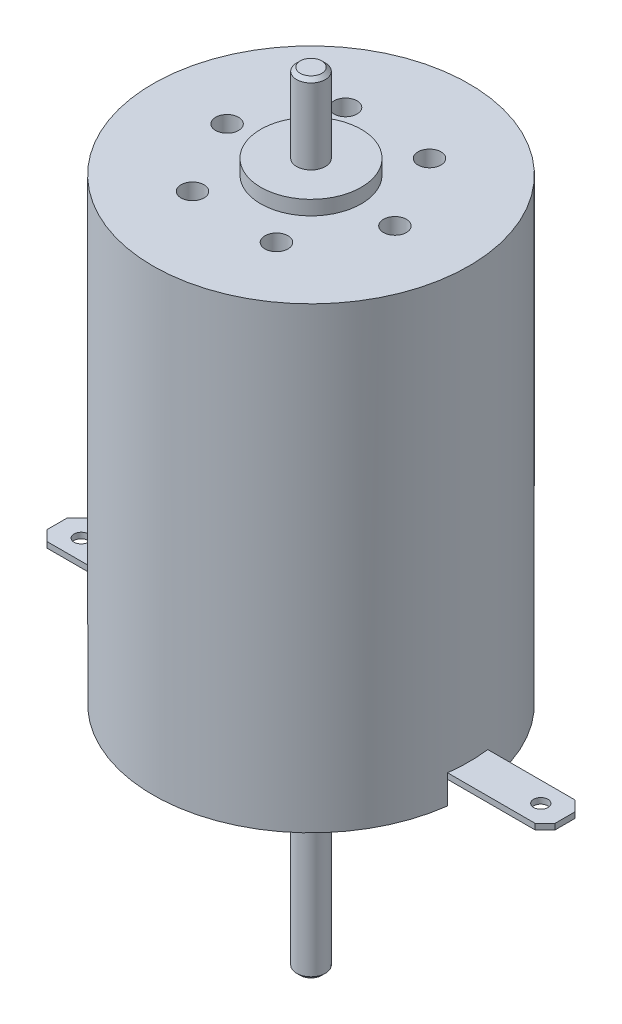
SolidWorks part; units mm, degrees
ref_plane "Face" through (0, 0, 0) normal (0, 0, 1) x (1, 0, 0)
ref_plane "Dessus" through (0, 0, 0) normal (0, 1, 0) x (1, 0, 0)
ref_plane "Droite" through (0, 0, 0) normal (1, 0, 0) x (0, 0, -1)
sketch "Esquisse1" plane through (0, 0, 0) normal (0, 1, 0) x (1, 0, 0)
  circle A0 centre (0, 0) radius 11
  dimension "D1" = 22
extrude "Extrusion1" add sketch "Esquisse1" along normal blind 31.9
sketch "Esquisse2" plane through (0, 31.9, 0) normal (0, 1, 0) x (1, 0, 0)
  circle A0 centre (0, 0) radius 3.5
  circle A1 centre (0, 0) radius 11 construction
  dimension "D1" = 7
extrude "Extrusion2" add sketch "Esquisse2" along normal blind 1
sketch "Esquisse3" plane through (0, 32.9, 0) normal (0, 1, 0) x (1, 0, 0)
  circle A0 centre (0, 0) radius 1
  circle A1 centre (0, 0) radius 3.5 construction
  dimension "D1" = 2
extrude "Extrusion3" add sketch "Esquisse3" along normal blind 5.5
chamfer "Chanfrein1" distance 0.25 angle 45 1 edges at (0, 38.4, 1)
sketch "Esquisse4" plane through (0, 0, 0) normal (0, -1, 0) x (1, 0, 0)
  circle A0 centre (0, 0) radius 4
  dimension "D1" = 8
extrude "Extrusion4" add sketch "Esquisse4" along normal blind 2.5
sketch "Esquisse5" plane through (0, -2.5, 0) normal (0, -1, 0) x (1, 0, 0)
  circle A0 centre (0, 0) radius 1
  dimension "D1" = 2
extrude "Extrusion5" add sketch "Esquisse5" along normal blind 13.5
hole_wizard "Trou taraudé M2x0.41" positions "Esquisse8" profile "Esquisse7" tap size "M2x0.4" standard "Ansi Métrique"
sketch "Esquisse8" plane through (0, 31.9, 0) normal (0, 1, 0) x (-1, 0, 0)
  point P0 (2.8652, -5.2717)
  dimension "D1" = 6
sketch "Esquisse7" plane through (-2.8652, 31.9, -5.2717) normal (1, 0, 0) x (0, 0, 1)
  line L0 (0, 0) -> (0, 4.4807)
  line L1 (0, 4.4807) -> (0.8, 4)
  line L2 (0.8, 4) -> (0.8, 0)
  line L5 (0.8, 0) -> (0, 0)
  line L10 (0, 4.4807) -> (-0.8, 4) construction
  line L11 (0, -6.35) -> (0, 107.95) construction
  dimension "Diamètre du trou pour taraudage" = 1.6
  dimension "Profondeur du trou pour taraudage" = 4
  dimension "Angle de pointe" = 118
cosmetic thread "Filetage de perçage1" parameters "D1"=4, "D2"=2
pattern_circular "Répétition circulaire1" count 6 every 60 about axis through (0, 0, 0) along (0, 1, 0) of "Trou taraudé M2x0.41"
chamfer "Chanfrein2" distance 0.25 angle 45 1 edges at (0, -16, -1)
sketch "Esquisse14" plane through (0, 0, 0) normal (0, -1, 0) x (1, 0, 0)
  line L0 (0, 0) -> (-13.6996, 0) construction
  line L1 (-11.917, 1.4) -> (-8.5, 1.4)
  line L2 (-11.917, 1.4) -> (-11.917, -1.4)
  line L3 (-11.917, -1.4) -> (-8.5, -1.4)
  line L4 (-8.5, 1.4) -> (-8.5, -1.4)
  circle A0 centre (0, 0) radius 11 construction
  dimension "D3" = 8.5
  dimension "D1" = 1.4
  dimension "D2" = 2.8
extrude "Enlèv. mat.-Extru.5" cut sketch "Esquisse14" against normal blind 2
pattern_circular "Répétition circulaire2" count 2 every 180 about axis through (0, 0, 0) along (0, 1, 0) of "Enlèv. mat.-Extru.5"
sketch "Esquisse16" plane through (8.5, 0, 0) normal (1, 0, 0) x (0, 0, -1)
  line L0 (1.4, 2) -> (1.4, 0) construction
  line L1 (-1.4, 2) -> (1.4, 2)
  line L2 (-1.4, 2) -> (-1.4, 1.6)
  line L3 (-1.4, 1.6) -> (1.4, 1.6)
  line L4 (1.4, 2) -> (1.4, 1.6)
  dimension "D1" = 0.4
extrude "Extrusion7" add sketch "Esquisse16" along normal blind 9.2
sketch "Esquisse17" plane through (-8.5, 0, 0) normal (-1, 0, 0) x (0, 0, 1)
  line L0 (1.4, 2) -> (1.4, 0) construction
  line L1 (-1.4, 2) -> (1.4, 2)
  line L2 (-1.4, 2) -> (-1.4, 1.6)
  line L3 (-1.4, 1.6) -> (1.4, 1.6)
  line L4 (1.4, 2) -> (1.4, 1.6)
  dimension "D1" = 0.4
extrude "Extrusion8" add sketch "Esquisse17" along normal blind 9.2
chamfer "Chanfrein3" distance 0.7 angle 45 2 edges at (17.7, 1.8, -1.4) (17.7, 1.8, 1.4)
chamfer "Chanfrein4" distance 0.7 angle 45 2 edges at (-17.7, 1.8, -1.4) (-17.7, 1.8, 1.4)
sketch "Esquisse18" plane through (0, 1.6, 0) normal (0, -1, 0) x (1, 0, 0)
  circle A0 centre (-16, 0) radius 0.5
  dimension "D2" = 1
  dimension "D1" = 16
extrude "Enlèv. mat.-Extru.6" cut sketch "Esquisse18" against normal through all
sketch "Esquisse19" plane through (0, 1.6, 0) normal (0, -1, 0) x (1, 0, 0)
  circle A0 centre (16, 0) radius 0.5
  dimension "D1" = 1
  dimension "D2" = 16
extrude "Enlèv. mat.-Extru.7" cut sketch "Esquisse19" against normal through all
